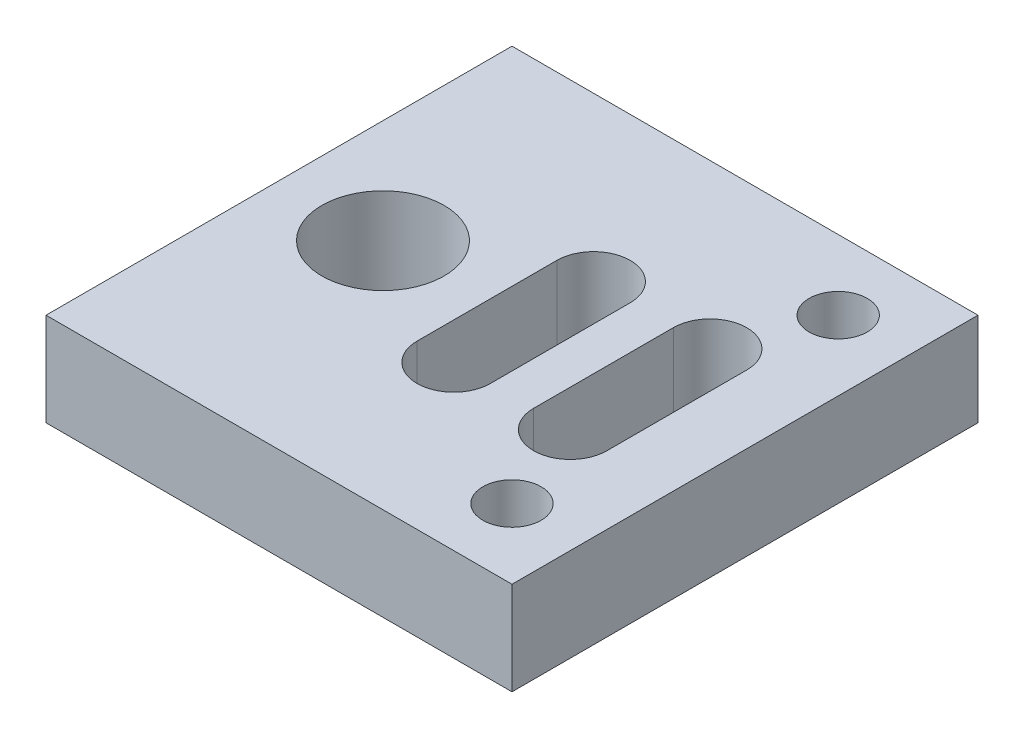
SolidWorks part; units mm, degrees
material "ABS"
ref_plane "Front Plane" through (0, 0, 0) normal (0, 0, 1) x (1, 0, 0)
ref_plane "Top Plane" through (0, 0, 0) normal (0, 1, 0) x (1, 0, 0)
ref_plane "Right Plane" through (0, 0, 0) normal (1, 0, 0) x (0, 0, -1)
sketch "Sketch1" plane through (0, 0, 0) normal (0, 1, 0) x (1, 0, 0)
  line L0 (15.5, 7) -> (15.5, 13) construction
  line L1 (13.925, 7) -> (13.925, 13)
  line L2 (10.5, 7) -> (10.5, 13) construction
  line L3 (8.925, 7) -> (8.925, 13)
  line L4 (20, 0) -> (20, 20)
  line L5 (20, 20) -> (0, 20)
  line L6 (0, 20) -> (0, 0)
  line L7 (0, 0) -> (20, 0)
  line L8 (0, 10) -> (20, 10) construction
  line L9 (12.075, 7) -> (12.075, 13)
  line L10 (17.075, 7) -> (17.075, 13)
  circle A0 centre (17, 17) radius 1.25
  arc A1 (13.925, 7) -> (17.075, 7) centre (15.5, 7) ccw
  arc A2 (17.075, 13) -> (13.925, 13) centre (15.5, 13) ccw
  circle A3 centre (4.4625, 10) radius 2.625
  arc A4 (8.925, 7) -> (12.075, 7) centre (10.5, 7) ccw
  arc A5 (12.075, 13) -> (8.925, 13) centre (10.5, 13) ccw
  circle A6 centre (17, 3) radius 1.25
  point P4 (15.5, 10)
  point P12 (10.5, 10)
  dimension "D3" = 2.5
  dimension "D4" = 5.25
  dimension "D7" = 1.5
  dimension "D9" = 1.575
  dimension "D1" = 20
  dimension "D2" = 20
  dimension "D5" = 14
  dimension "D6" = 3
  dimension "D8" = 5
  dimension "D10" = 6
  dimension "D11" = 4.4625
extrude "Boss-Extrude1" add sketch "Sketch1" against normal blind 4
